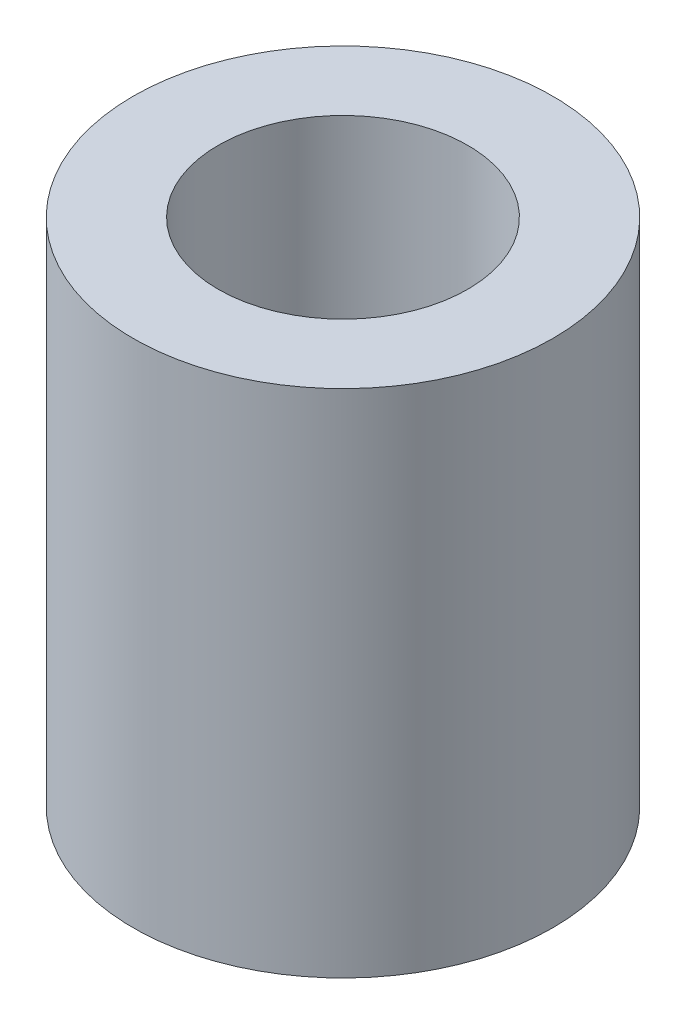
SolidWorks part; units mm, degrees
material "ABS"
ref_plane "Front Plane" through (0, 0, 0) normal (0, 0, 1) x (1, 0, 0)
ref_plane "Top Plane" through (0, 0, 0) normal (0, 1, 0) x (1, 0, 0)
ref_plane "Right Plane" through (0, 0, 0) normal (1, 0, 0) x (0, 0, -1)
sketch "Sketch1" plane through (0, 0, 0) normal (0, 1, 0) x (1, 0, 0)
  circle A0 centre (0, 0) radius 4.4
  dimension "D1" = 8.8
extrude "Extrude-Thin1" add sketch "Sketch1" along normal blind 18 thin
